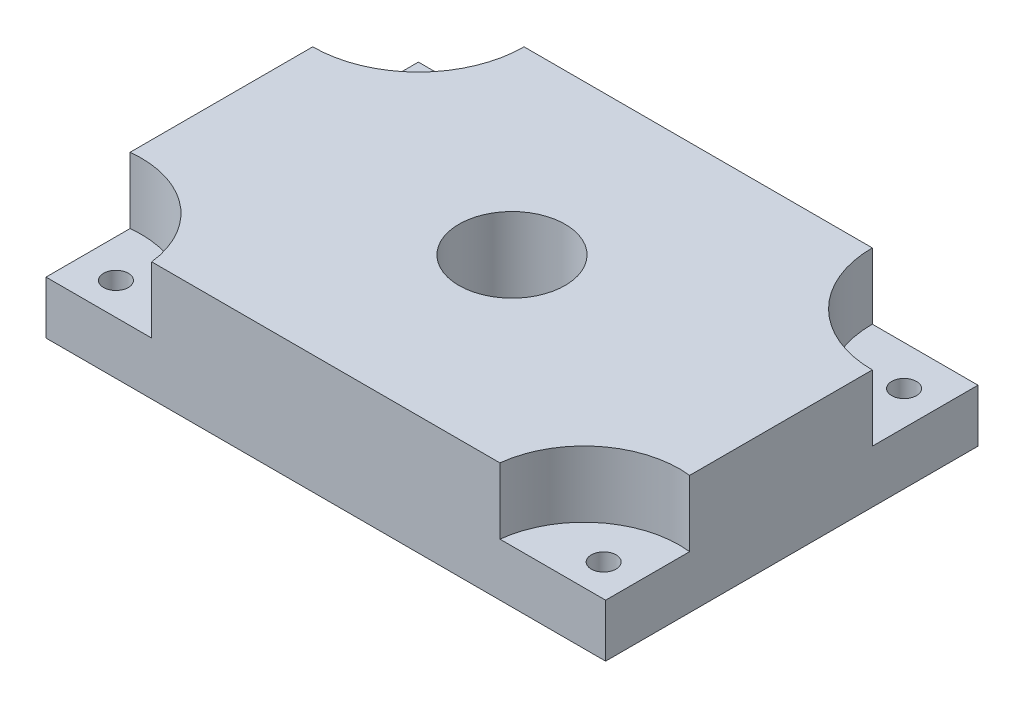
SolidWorks part; units mm, degrees
ref_plane "Front Plane" through (0, 0, 0) normal (0, 0, 1) x (1, 0, 0)
ref_plane "Top Plane" through (0, 0, 0) normal (0, 1, 0) x (1, 0, 0)
ref_plane "Right Plane" through (0, 0, 0) normal (1, 0, 0) x (0, 0, -1)
sketch "Sketch1" plane through (0, 0, 0) normal (0, 1, 0) x (1, 0, 0)
  line L1 (-13.45, 8.95) -> (13.45, 8.95)
  line L2 (-13.45, 8.95) -> (-13.45, -8.95)
  line L3 (-13.45, -8.95) -> (13.45, -8.95)
  line L4 (13.45, 8.95) -> (13.45, -8.95)
  line L5 (-13.45, 8.95) -> (13.45, -8.95) construction
  line L6 (-13.45, -8.95) -> (13.45, 8.95) construction
  point P0 (0, 0)
extrude "Boss-Extrude1" add sketch "Sketch1" along normal blind 2.54
sketch "Sketch2" plane through (0, 2.54, 0) normal (0, 1, 0) x (1, 0, 0)
  line L2 (-13.45, -8.95) -> (13.45, -8.95) construction
  line L3 (-13.45, 8.95) -> (-13.45, -8.95) construction
  line L4 (-8.37, -8.95) -> (8.37, -8.95)
  line L5 (13.45, 8.95) -> (-13.45, 8.95) construction
  line L6 (-13.45, 3.87) -> (-13.45, -4.9106)
  line L7 (-8.37, 8.95) -> (8.37, 8.95)
  line L8 (13.45, -8.95) -> (13.45, 8.95) construction
  line L9 (13.45, 3.87) -> (13.45, -4.9106)
  arc A1 (-13.45, 3.87) -> (-8.37, 8.95) centre (-13.45, 8.95) ccw
  arc A2 (8.37, 8.95) -> (13.45, 3.87) centre (13.45, 8.95) ccw
  arc A3 (13.45, -4.9106) -> (8.37, -8.95) centre (12.9297, -9.4703) ccw
  arc A4 (-13.45, -4.9106) -> (-8.37, -8.95) centre (-12.9297, -9.4703) cw
extrude "Boss-Extrude2" add sketch "Sketch2" along normal blind 3.175
hole_wizard "1/4-20 Tapped Hole1" positions "Sketch3" profile "Sketch4" tap size "1/4-20" standard "ANSI Inch" end condition up to next
sketch "Sketch3" plane through (0, 5.715, 0) normal (0, 1, 0) x (1, 0, 0)
  point P0 (0, 0)
sketch "Sketch4" plane through (0, 5.715, 0) normal (1, 0, 0) x (0, 0, 1)
  line L0 (0, 0) -> (0, 5.715)
  line L1 (0, 5.715) -> (2.5527, 5.715)
  line L2 (2.5527, 5.715) -> (2.5527, 0)
  line L5 (2.5527, 0) -> (0, 0)
  line L11 (0, -6.35) -> (0, 107.95) construction
  dimension "Thru Tap Drill Dia." = 5.1054
  dimension "Thru Tap Drill Depth" = 5.715
cosmetic thread "Hole Thread1" parameters "D2"=6.35
sketch "Sketch10" plane through (0, 2.54, 0) normal (0, 1, 0) x (1, 0, 0)
  line L0 (-13.45, 8.95) -> (-10.0382, 5.5382)
  line L1 (13.45, 8.95) -> (9.8579, 5.3579)
  line L2 (-13.45, -8.95) -> (-10.0734, -5.8782)
  line L3 (13.45, -8.95) -> (10.0734, -5.8782)
  arc A0 (8.37, 8.95) -> (13.45, 3.87) centre (13.45, 8.95) ccw construction
  arc A1 (-8.37, -8.95) -> (-13.45, -4.9106) centre (-12.9297, -9.4703) ccw construction
  arc A2 (13.45, -4.9106) -> (8.37, -8.95) centre (12.9297, -9.4703) ccw construction
hole_wizard "3/64 (0.04688) Diameter Hole1" positions "Sketch11" profile "Sketch12" hole size "3/64" standard "ANSI Inch" end condition up to next
sketch "Sketch11" plane through (0, 2.54, 0) normal (0, 1, 0) x (1, 0, 0)
  point P0 (-11.6307, 7.0331)
  point P2 (-11.6307, -7.4069)
  point P4 (11.8134, -7.4069)
  point P6 (11.8134, 7.0331)
sketch "Sketch12" plane through (-11.6307, 2.54, -7.0331) normal (1, 0, 0) x (0, 0, 1)
  line L0 (0, 0) -> (0, 2.54)
  line L1 (0, 2.54) -> (0.5954, 2.54)
  line L2 (0.5954, 2.54) -> (0.5954, 0)
  line L5 (0.5954, 0) -> (0, 0)
  line L11 (0, -6.35) -> (0, 107.95) construction
  dimension "Thru Hole Dia." = 1.1908
  dimension "Thru Hole Depth" = 2.54
